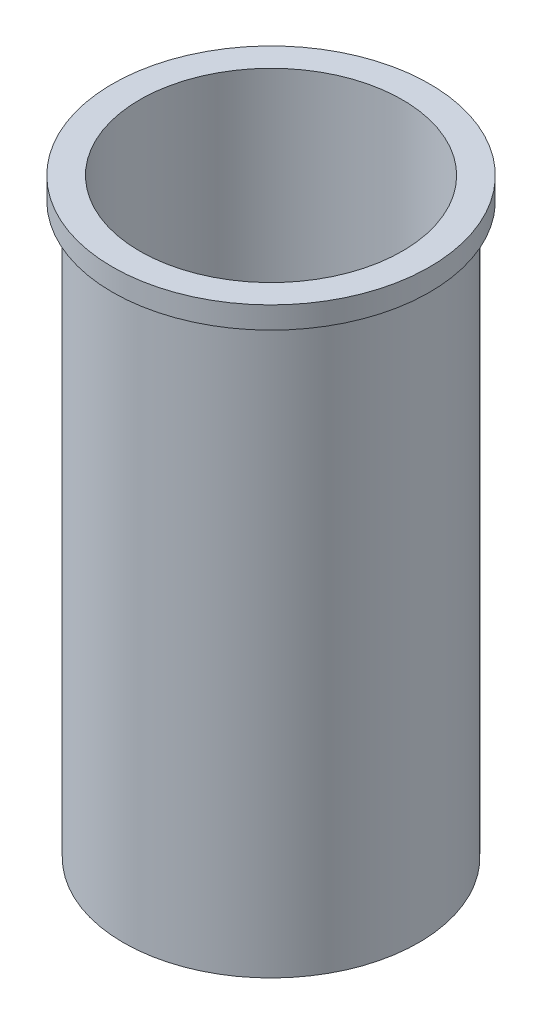
SolidWorks part; units mm, degrees
ref_plane "Front Plane" through (0, 0, 0) normal (0, 0, 1) x (1, 0, 0)
ref_plane "Top Plane" through (0, 0, 0) normal (0, 1, 0) x (1, 0, 0)
ref_plane "Right Plane" through (0, 0, 0) normal (1, 0, 0) x (0, 0, -1)
sketch "Sketch1" plane through (0, 0, 0) normal (0, 1, 0) x (1, 0, 0)
  circle A0 centre (0, 0) radius 6
  circle A1 centre (0, 0) radius 6.75
  dimension "D1" = 12
  dimension "D2" = 13.5
extrude "Boss-Extrude1" add sketch "Sketch1" along normal blind 27
sketch "Sketch2" plane through (0, 27, 0) normal (0, 1, 0) x (1, 0, 0)
  circle A0 centre (0, 0) radius 7.25
  circle A1 centre (0, 0) radius 6.75 construction
  circle A2 centre (0, 0) radius 6.75
  dimension "D1" = 14.5
extrude "Boss-Extrude2" add sketch "Sketch2" against normal blind 1
